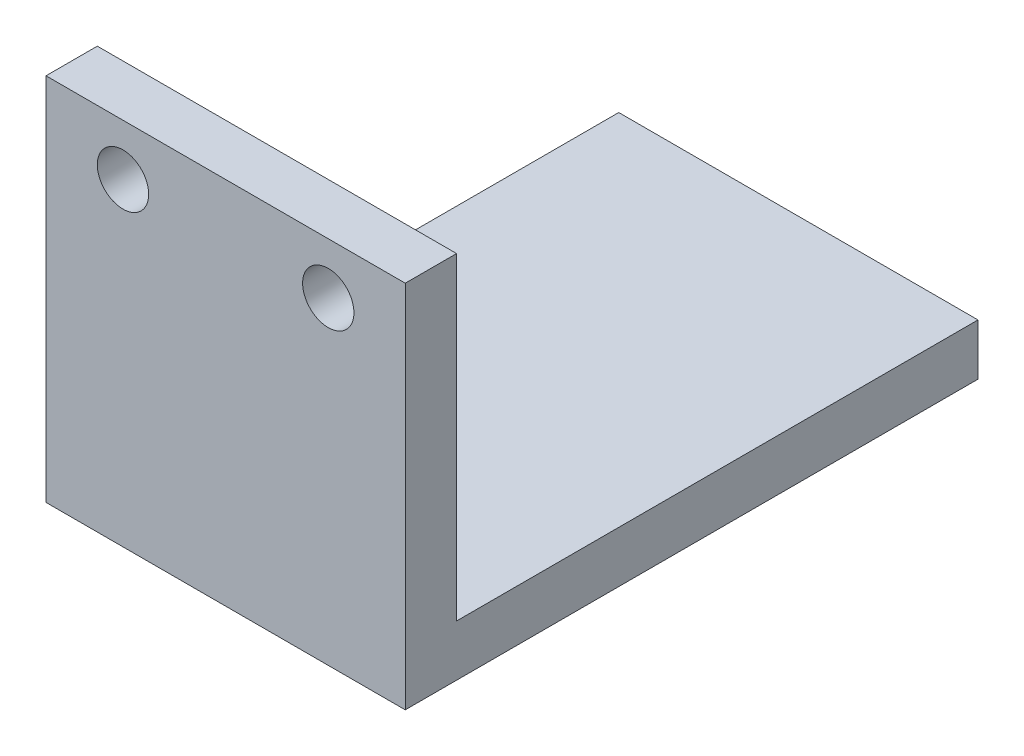
SolidWorks part; units mm, degrees
material "Plain Carbon Steel"
ref_plane "Front Plane" through (0, 0, 0) normal (0, 0, 1) x (1, 0, 0)
ref_plane "Top Plane" through (0, 0, 0) normal (0, 1, 0) x (1, 0, 0)
ref_plane "Right Plane" through (0, 0, 0) normal (1, 0, 0) x (0, 0, -1)
sketch "Sketch1" plane through (0, 0, 0) normal (0, 0, 1) x (1, 0, 0)
  line L0 (-10, 0) -> (10, 0) construction
  line L1 (-17.5, 5) -> (17.5, 5)
  line L2 (-17.5, 5) -> (-17.5, -5)
  line L3 (-17.5, -5) -> (17.5, -5) construction
  line L4 (17.5, 5) -> (17.5, -5)
  line L6 (-17.5, -5) -> (17.5, -5) construction
  line L7 (-17.5, -5) -> (-17.5, -26)
  line L8 (-17.5, -26) -> (17.5, -26)
  line L9 (17.5, -5) -> (17.5, -26)
  circle A0 centre (-10, 0) radius 2.5
  circle A1 centre (10, 0) radius 2.5
  point P4 (0, 5)
  point P10 (0, 0)
  point P13 (-17.5, 0)
  dimension "D2" = 5
  dimension "D1" = 20
  dimension "D3" = 5
  dimension "D4" = 35
  dimension "D5" = 21
extrude "Boss-Extrude1" add sketch "Sketch1" along normal blind 5
sketch "Sketch2" plane through (0, -26, 0) normal (0, -1, 0) x (1, 0, 0)
  line L0 (17.5, 5) -> (17.5, 0) construction
  line L1 (-17.5, 5) -> (17.5, 5)
  line L2 (-17.5, 5) -> (-17.5, -50.8)
  line L3 (-17.5, -50.8) -> (17.5, -50.8)
  line L4 (17.5, 5) -> (17.5, -50.8)
  line L5 (-17.5, 0) -> (17.5, 0) construction
  line L6 (-12.5, 0) -> (-12.5, -50.8) construction
  circle A0 centre (-12.5, -22.4) radius 1.25
  point P13 (-12.5, -25.4)
  dimension "D2" = 2.5
  dimension "D1" = 50.8
  dimension "D3" = 5
  dimension "D4" = 3
extrude "Boss-Extrude2" add sketch "Sketch2" along normal blind 5
